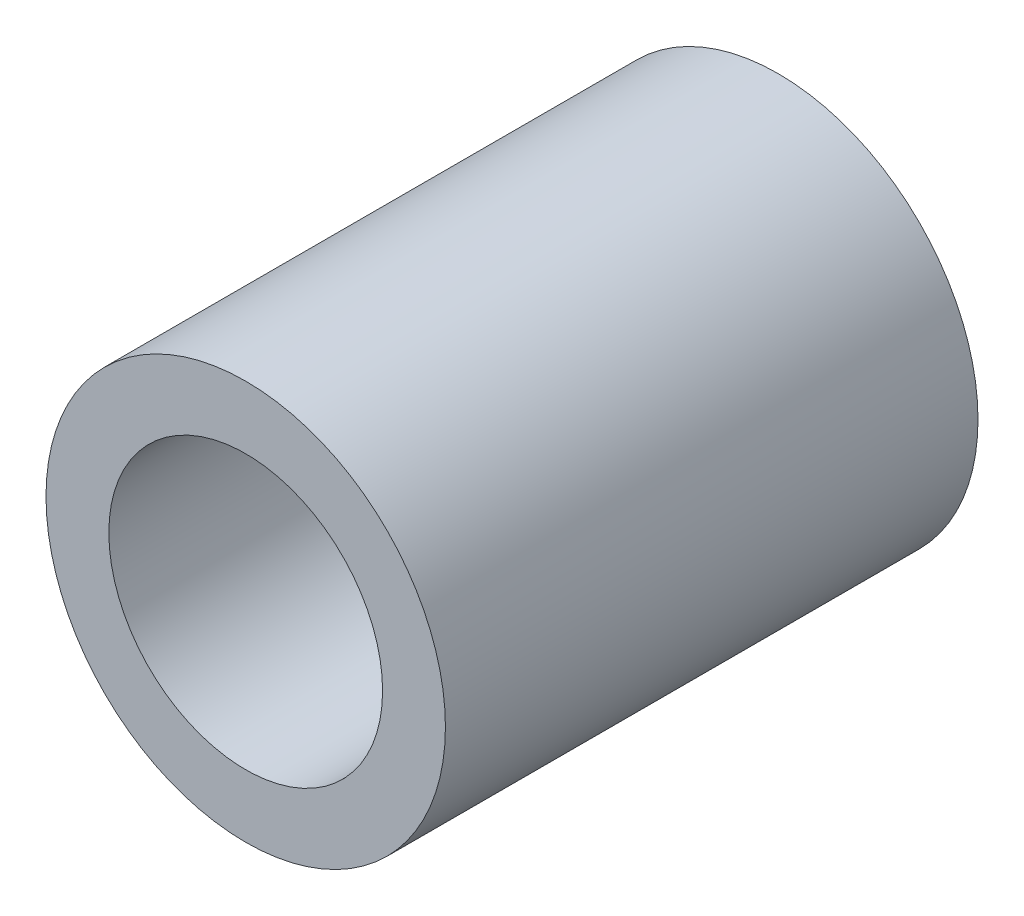
SolidWorks part; units mm, degrees
ref_plane "Front Plane" through (0, 0, 0) normal (0, 0, 1) x (1, 0, 0)
ref_plane "Top Plane" through (0, 0, 0) normal (0, 1, 0) x (1, 0, 0)
ref_plane "Right Plane" through (0, 0, 0) normal (1, 0, 0) x (0, 0, -1)
sketch "Sketch1" plane through (0, 0, 0) normal (0, 0, 1) x (1, 0, 0)
  circle A0 centre (0, 0) radius 2.3813
  dimension "D1" = 4.7625
extrude "Extrude1" add sketch "Sketch1" along normal mid plane 6.35
hole_wizard "#4 Clearance Hole1" positions "3DSketch1" profile "Sketch2" hole size "#4" standard "Ansi Inch"
sketch3d "3DSketch1"
  circle A0 centre (0, 0, 3.175) radius 2.3813 construction
  point P0 (0, 0, 3.175)
  point P7 (0, 0, 5.5563)
sketch "Sketch2" plane through (0, 0, 3.175) normal (1, 0, 0) x (0, -1, 0)
  line L0 (0, 0) -> (0, 7.3306)
  line L1 (0, 7.3306) -> (1.6319, 6.35)
  line L2 (1.6319, 6.35) -> (1.6319, 0)
  line L5 (1.6319, 0) -> (0, 0)
  line L10 (0, 7.3306) -> (-1.632, 6.35) construction
  line L11 (0, -6.35) -> (0, 107.95) construction
  dimension "Hole Dia." = 3.2639
  dimension "Hole Depth" = 6.35
  dimension "Drill Angle" = 118
